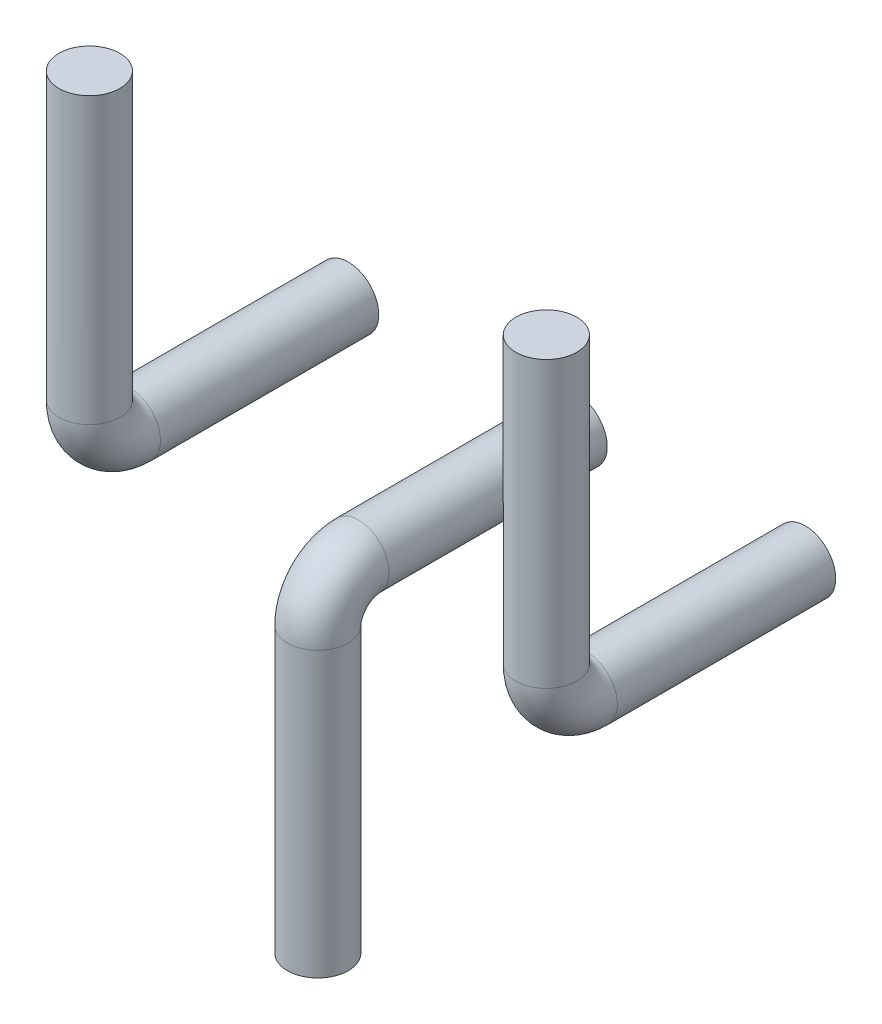
SolidWorks part; units mm, degrees
material "PP omopolimero"
ref_plane "Piano frontale" through (0, 0, 0) normal (0, 0, 1) x (1, 0, 0)
ref_plane "Piano superiore" through (0, 0, 0) normal (0, 1, 0) x (1, 0, 0)
ref_plane "Piano destro" through (0, 0, 0) normal (1, 0, 0) x (0, 0, -1)
sketch "Schizzo2" plane through (-55, -0.0508, 0) normal (-1, 0, 0) x (0, 0, 1)
  line L0 (0, 0) -> (21.5, 0)
  line L2 (25.5, 32.0508) -> (25.5, 4)
  arc A1 (25.5, 4) -> (21.5, 0) centre (21.5, 4) cw
  dimension "D1" = 4
sketch "Schizzo3" plane through (0, 0, 0) normal (0, 0, 1) x (1, 0, 0)
  circle A0 centre (-55, -0.0508) radius 3
  circle A1 centre (-10, -0.0508) radius 3
sweep "Sweep1" add profiles "Schizzo3" path "Schizzo2"
sketch "Schizzo4" plane through (-32.5, -0.0508, 0) normal (-1, 0, 0) x (0, 0, 1)
  line L0 (0, 0) -> (21.5, 0)
  line L2 (20.5, -31.9492) -> (30.5, -31.9492) construction
  line L3 (25.5, -31.9492) -> (25.5, -4)
  arc A0 (21.5, 0) -> (25.5, -4) centre (21.5, -4) cw
  dimension "D1" = 4
sketch "Schizzo5" plane through (0, 0, 0) normal (0, 0, 1) x (1, 0, 0)
  circle A0 centre (-32.5, -0.0508) radius 3
sweep "Sweep2" add profiles "Schizzo5" path "Schizzo4"
